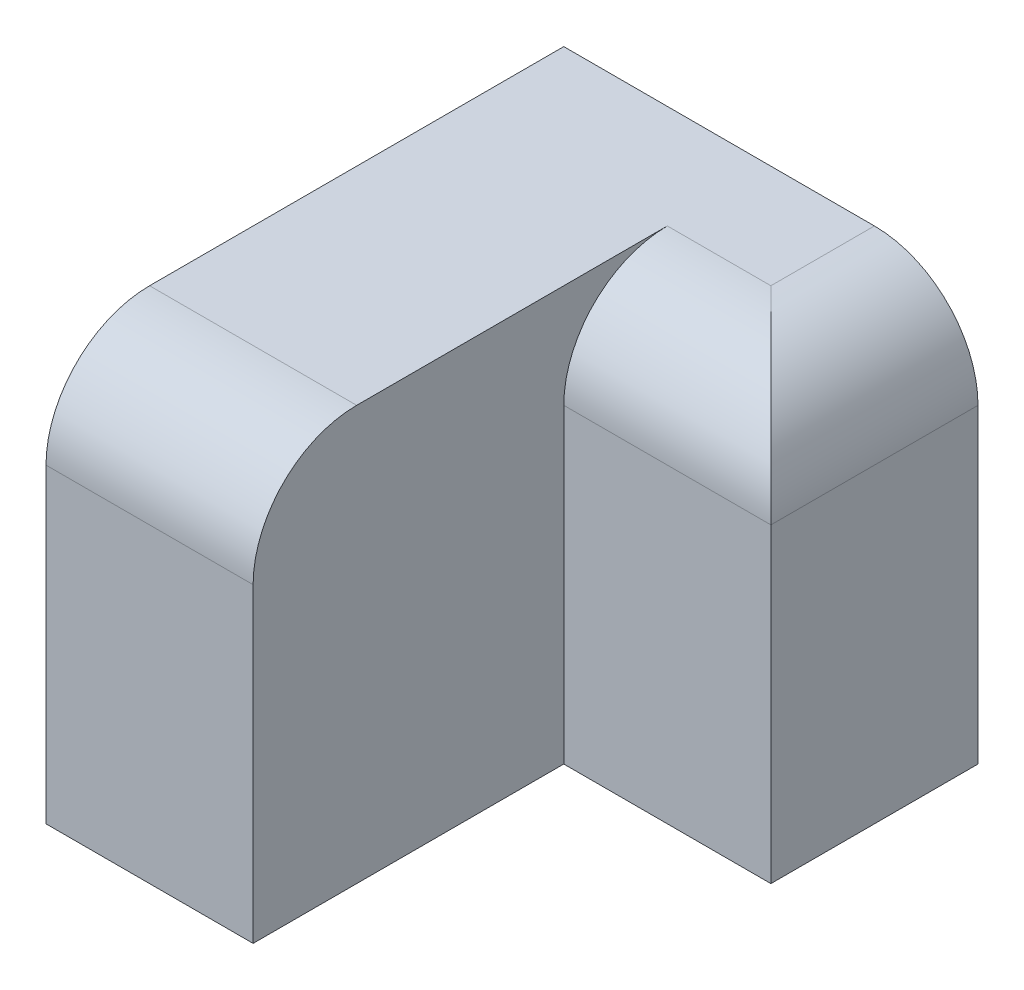
SolidWorks part; units mm, degrees
ref_plane "Front Plane" through (0, 0, 0) normal (0, 0, 1) x (1, 0, 0)
ref_plane "Top Plane" through (0, 0, 0) normal (0, 1, 0) x (1, 0, 0)
ref_plane "Right Plane" through (0, 0, 0) normal (1, 0, 0) x (0, 0, -1)
sketch "Sketch1" plane through (0, 0, 0) normal (0, 0, 1) x (1, 0, 0)
  line L1 (-30, -40) -> (-10, -40)
  line L2 (-10, -40) -> (-10, 0)
  line L3 (-10, 0) -> (-30, 0)
  line L4 (-30, 0) -> (-30, -40)
  dimension "D1" = 20
  dimension "Width" = 40
extrude "Boss-Extrude1" add sketch "Sketch1" along normal blind 30
sketch "Sketch2" plane through (0, 0, 0) normal (0, 0, 1) x (1, 0, 0)
  line L1 (-30, -40) -> (10, -40)
  line L2 (10, -40) -> (10, 0)
  line L3 (10, 0) -> (-30, 0)
  line L4 (-30, 0) -> (-30, -40)
  dimension "D1" = 40
  dimension "Width" = 40
extrude "Boss-Extrude2" add sketch "Sketch2" against normal blind 20
fillet "Fillet1" radius 10 3 edges at (0, 0, 0) (10, 0, -10) (-20, 0, 30)
